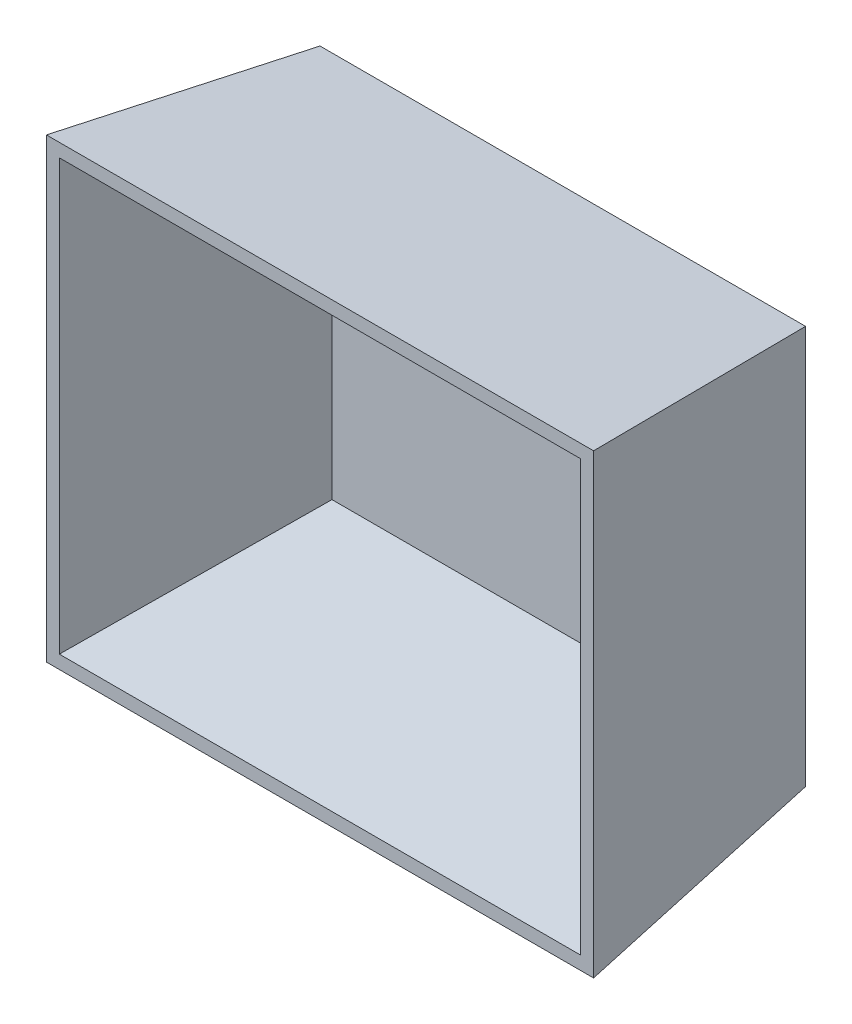
SolidWorks part; units mm, degrees
ref_plane "Front" through (0, 0, 0) normal (0, 0, 1) x (1, 0, 0)
ref_plane "Top" through (0, 0, 0) normal (0, 1, 0) x (1, 0, 0)
ref_plane "Right" through (0, 0, 0) normal (1, 0, 0) x (0, 0, -1)
sketch "草图1" plane through (0, 0, 0) normal (0, 0, 1) x (1, 0, 0)
  line L1 (0, 0) -> (134, 0)
  line L2 (0, 0) -> (0, 110)
  line L3 (0, 110) -> (134, 110)
  line L4 (134, 0) -> (134, 110)
ref_plane "基准面1" through (0, 0, 67) normal (0, 0, 1) x (1, 0, 0)
sketch "草图2" plane through (0, 0, 67) normal (0, 0, 1) x (1, 0, 0)
  line L1 (-8.5, -8) -> (142.5, -8)
  line L2 (-8.5, -8) -> (-8.5, 118)
  line L3 (-8.5, 118) -> (142.5, 118)
  line L4 (142.5, -8) -> (142.5, 118)
  line L5 (67, 118) -> (67, -8) construction
  line L6 (-8.5, 55) -> (142.5, 55) construction
  point P0 (67, 55)
  point P4 (0, 0)
loft "放样2" add profiles "草图2", "草图1"
sketch "草图3" plane through (0, 0, 67) normal (0, 0, 1) x (1, 0, 0)
  line L1 (-4.9379, -4.3136) -> (138.9379, -4.3136)
  line L2 (-4.9379, -4.3136) -> (-4.9379, 114.3136)
  line L3 (-4.9379, 114.3136) -> (138.9379, 114.3136)
  line L4 (138.9379, -4.3136) -> (138.9379, 114.3136)
  line L5 (67, 114.3136) -> (67, -4.3136) construction
  line L6 (-4.9379, 55) -> (138.9379, 55) construction
  point P0 (67, 55)
ref_plane "基准面2" through (0, 0, 1) normal (0, 0, -1) x (-1, 0, 0)
sketch "草图4" plane through (0, 0, 1) normal (0, 0, -1) x (-1, 0, 0)
  line L0 (-67, 114.3136) -> (-67, -4.3136) construction
  line L1 (-4.2964, 105.7682) -> (-129.7036, 105.7682)
  line L2 (-4.2964, 105.7682) -> (-4.2964, 4.2318)
  line L3 (-4.2964, 4.2318) -> (-129.7036, 4.2318)
  line L4 (-129.7036, 105.7682) -> (-129.7036, 4.2318)
  line L5 (-67, 4.2318) -> (-67, 105.7682) construction
  line L6 (-4.2964, 55) -> (-129.7036, 55) construction
  point P0 (-67, 55)
loft "切除-放样3" cut profiles "草图3", "草图4"
